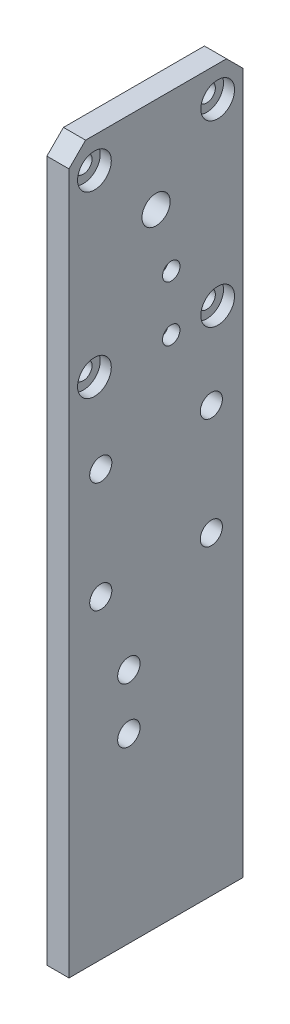
SolidWorks part; units mm, degrees
ref_plane "Alzado" through (0, 0, 0) normal (0, 0, 1) x (1, 0, 0)
ref_plane "Planta" through (0, 0, 0) normal (0, 1, 0) x (1, 0, 0)
ref_plane "Vista lateral" through (0, 0, 0) normal (1, 0, 0) x (0, 0, -1)
sketch "Croquis1" plane through (0, 0, 0) normal (1, 0, 0) x (0, 0, -1)
  line L1 (-15.75, -63) -> (15.75, -63)
  line L2 (-15.75, -63) -> (-15.75, 63)
  line L3 (-15.75, 63) -> (15.75, 63)
  line L4 (15.75, -63) -> (15.75, 63)
  line L5 (-15.75, -63) -> (15.75, 63) construction
  line L6 (-15.75, 63) -> (15.75, -63) construction
  point P0 (0, 0)
  dimension "D1" = 31.5
  dimension "D2" = 126
extrude "Saliente-Extruir1" add sketch "Croquis1" along normal blind 4
sketch "Croquis3" plane through (4, 0, 0) normal (1, 0, 0) x (0, 0, -1)
  line L0 (-10, 10.1) -> (10, 10.1) construction
  line L2 (15.75, 63) -> (-15.75, 63) construction
  line L4 (-10, 10.1) -> (-10, -9.9) construction
  circle A0 centre (-10, 10.1) radius 2
  circle A1 centre (10, 10.1) radius 2
  circle A2 centre (0, 10.1) radius 2 construction
  circle A3 centre (-10, -9.9) radius 2
  circle A4 centre (0, -9.9) radius 2 construction
  circle A5 centre (10, -9.9) radius 2
  dimension "D2" = 4
  dimension "D1" = 52.9
  dimension "D3" = 20
  dimension "D5" = 20
  dimension "D4" = 2
extrude "Cortar-Extruir2" cut sketch "Croquis3" against normal through all
sketch "Croquis8" plane through (0, 0, 0) normal (-1, 0, 0) x (0, 0, 1)
  line L1 (0, 45.75) -> (0, 10.1) construction
  line L2 (0, 10.1) -> (10, 10.1) construction
  circle A0 centre (0, 45.75) radius 2.55
  dimension "D2" = 5.1
  dimension "D1" = 35.65
extrude "Cortar-Extruir3" cut sketch "Croquis8" against normal through all
sketch "Croquis11" plane through (4, 0, 0) normal (1, 0, 0) x (0, 0, -1)
  line L0 (15.75, -63) -> (15.75, 63) construction
  line L2 (-10, 10.1) -> (10, 10.1) construction
  line L3 (2.75, 24.75) -> (2.75, 10.1) construction
  line L8 (2.75, 34.75) -> (2.75, 24.75) construction
  circle A4 centre (2.75, 34.75) radius 1.575
  circle A5 centre (2.75, 24.75) radius 1.575
  dimension "D1" = 13
  dimension "D3" = 3.15
  dimension "D2" = 14.65
  dimension "D4" = 10
extrude "Cortar-Extruir8" cut sketch "Croquis11" against normal through all
sketch "Croquis15" plane through (4, 0, 0) normal (1, 0, 0) x (0, 0, -1)
  line L0 (-11.15, 57.45) -> (11.15, 25.1) construction
  line L1 (-11.15, 57.45) -> (11.15, 57.45) construction
  line L2 (-11.15, 57.45) -> (-11.15, 25.1) construction
  line L3 (-11.15, 25.1) -> (11.15, 25.1) construction
  line L4 (11.15, 57.45) -> (11.15, 25.1) construction
  line L5 (0, 41.275) -> (0, 45.75) construction
  line L6 (-15.86, 54.7) -> (22.092, 54.7) construction
  line L7 (-15.75, 63) -> (-15.75, -63) construction
  line L8 (-10, 10.1) -> (10, 10.1) construction
  line L9 (10, 10.1) -> (10, 20.1) construction
  line L10 (10, 20.1) -> (-10, 20.1) construction
  line L11 (-12.725, 57.45) -> (-12.725, 70.4928) construction
  line L13 (-23.8132, 53.7) -> (25.052, 53.7) construction
  line L14 (-11.15, 59.025) -> (-6.2662, 59.025) construction
  circle A0 centre (-11.15, 57.45) radius 1.575
  circle A1 centre (11.15, 57.45) radius 1.575
  circle A2 centre (-11.15, 25.1) radius 1.575
  circle A3 centre (11.15, 25.1) radius 1.575
  circle A4 centre (0, 45.75) radius 7.95 construction
  circle A5 centre (-11.15, 57.45) radius 1.5 construction
  circle A6 centre (-11.15, 57.45) radius 2.75 construction
  circle A9 centre (0, 45.75) radius 6 construction
  dimension "D1" = 3.15
  dimension "D2" = 15.9
  dimension "D3" = 3
  dimension "D8" = 1
  dimension "D4" = 12
  dimension "D10" = 5.5
  dimension "D5" = 4.6
  dimension "D6" = 10
  dimension "D7" = 5
extrude "Cortar-Extruir11" cut sketch "Croquis15" against normal through all
chamfer "Chaflán2" distance 3 angle 45 2 edges at (2, 63, -15.75) (2, 63, 15.75)
sketch "Croquis19" plane through (0, 0, 0) normal (-1, 0, 0) x (0, 0, 1)
  circle A0 centre (-2.75, 24.75) radius 3.5
  circle A1 centre (-2.75, 34.75) radius 3.5
  dimension "D1" = 7
extrude "Cortar-Extruir13" cut sketch "Croquis19" against normal blind 1.9
sketch "Croquis20" plane through (4, 0, 0) normal (1, 0, 0) x (0, 0, -1)
  circle A0 centre (-11.15, 57.45) radius 3.05
  circle A1 centre (11.15, 57.45) radius 3.05
  circle A2 centre (11.15, 25.1) radius 3.05
  circle A3 centre (-11.15, 25.1) radius 3.05
  dimension "D1" = 6.1
extrude "Cortar-Extruir14" cut sketch "Croquis20" against normal blind 2
sketch "Croquis24" plane through (4, 0, 0) normal (1, 0, 0) x (0, 0, -1)
  line L0 (-15.75, 60) -> (-15.75, -63) construction
  line L1 (-15.75, -63) -> (15.75, -63)
  line L2 (-15.75, -63) -> (-15.75, -66.76)
  line L3 (-15.75, -66.76) -> (15.75, -66.76)
  line L4 (15.75, -63) -> (15.75, -66.76)
  dimension "D1" = 3.76
extrude "Saliente-Extruir3" add sketch "Croquis24" against normal up to surface (4 mm away) up to face at (0, 34.75, 0.75)
sketch "Croquis25" plane through (4, 0, 0) normal (1, 0, 0) x (0, 0, -1)
  line L3 (-10.9173, -23.8913) -> (1.0827, -23.8913) construction
  line L4 (-13.0173, -33.8913) -> (3.1827, -33.8913) construction
  circle A0 centre (-4.9173, -23.8913) radius 2.025
  circle A1 centre (-4.9173, -33.8913) radius 2.025
  arc A2 (-10.9173, -31.7913) -> (-10.9173, -35.9913) centre (-10.9173, -33.8913) ccw construction
  arc A3 (1.0827, -35.9913) -> (1.0827, -31.7913) centre (1.0827, -33.8913) ccw construction
  dimension "D1" = 4.05
extrude "Cortar-Extruir15" cut sketch "Croquis25" against normal through all
